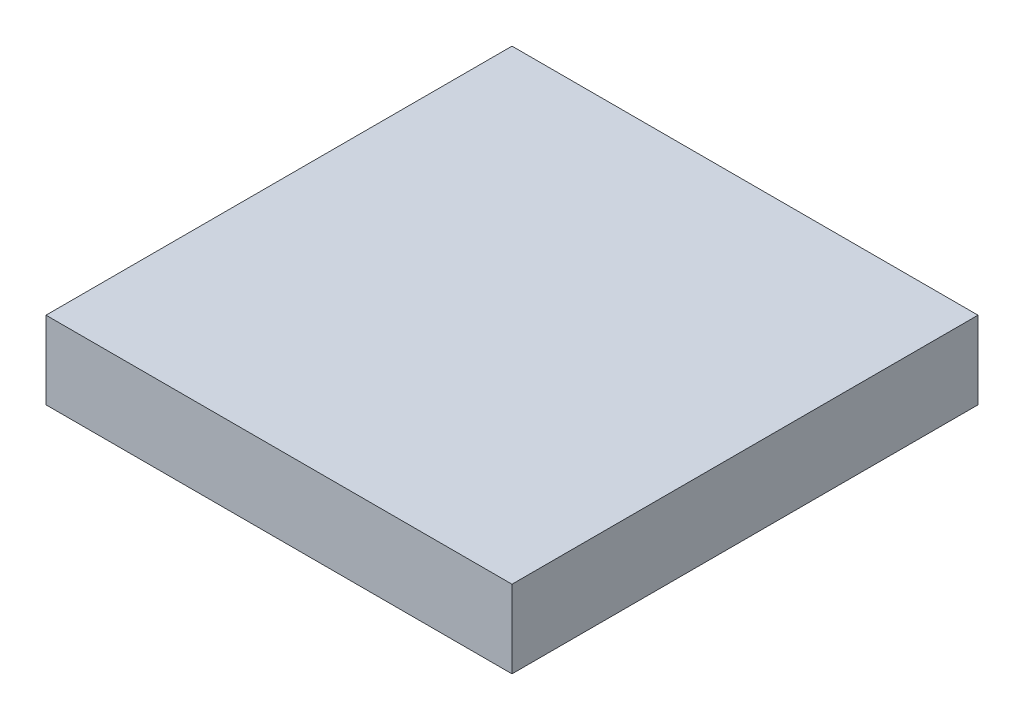
SolidWorks part; units mm, degrees
ref_plane "Front Plane" through (0, 0, 0) normal (0, 0, 1) x (1, 0, 0)
ref_plane "Top Plane" through (0, 0, 0) normal (0, 1, 0) x (1, 0, 0)
ref_plane "Right Plane" through (0, 0, 0) normal (1, 0, 0) x (0, 0, -1)
sketch "Sketch1" plane through (0, 0, 0) normal (0, 1, 0) x (1, 0, 0)
  line L1 (152.4, -152.4) -> (-152.4, -152.4)
  line L2 (152.4, -152.4) -> (152.4, 152.4)
  line L3 (152.4, 152.4) -> (-152.4, 152.4)
  line L4 (-152.4, -152.4) -> (-152.4, 152.4)
  line L5 (152.4, -152.4) -> (-152.4, 152.4) construction
  line L6 (152.4, 152.4) -> (-152.4, -152.4) construction
  point P0 (0, 0)
  dimension "D1" = 304.8
  dimension "D2" = 304.8
extrude "Boss-Extrude1" add sketch "Sketch1" along normal blind 50.8
